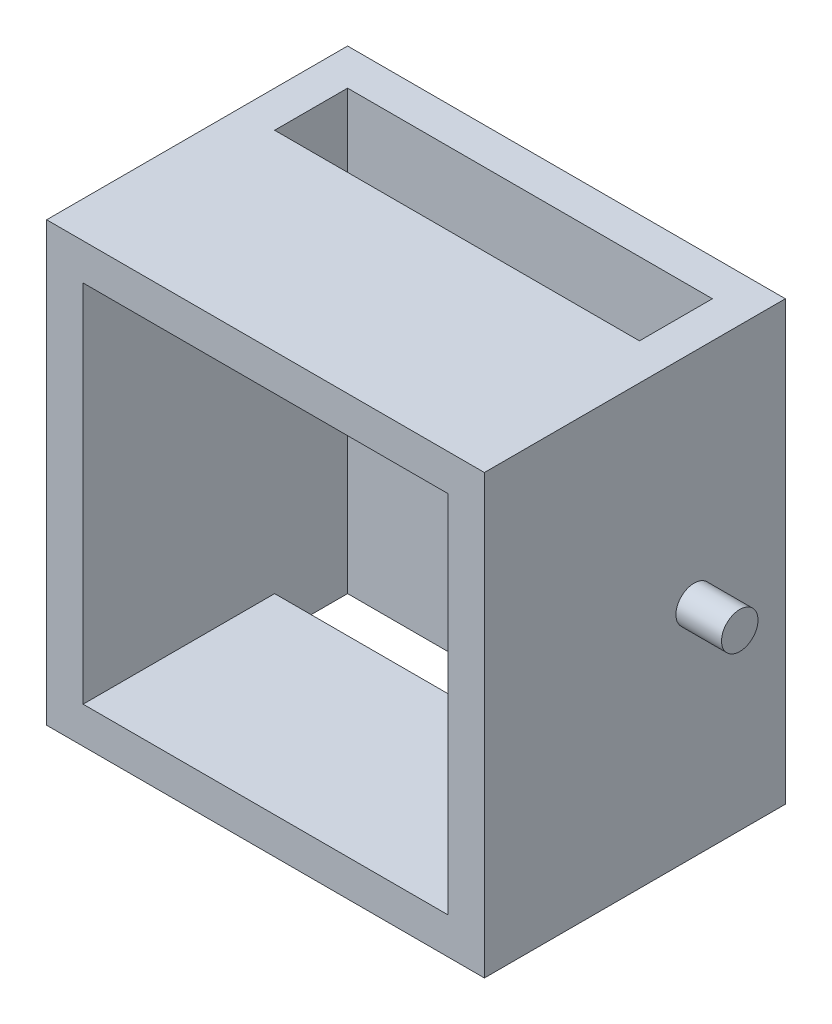
SolidWorks part; units mm, degrees
ref_plane "Front Plane" through (0, 0, 0) normal (0, 0, 1) x (1, 0, 0)
ref_plane "Top Plane" through (0, 0, 0) normal (0, 1, 0) x (1, 0, 0)
ref_plane "Right Plane" through (0, 0, 0) normal (1, 0, 0) x (0, 0, -1)
sketch "Sketch1" plane through (0, 0, 0) normal (0, 0, 1) x (1, 0, 0)
  line L1 (-24, -24) -> (24, -24)
  line L2 (-24, -24) -> (-24, 24)
  line L3 (-24, 24) -> (24, 24)
  line L4 (24, -24) -> (24, 24)
  line L5 (-24, -24) -> (24, 24) construction
  line L6 (-24, 24) -> (24, -24) construction
  point P0 (0, 0)
  dimension "D1" = 48
extrude "Boss-Extrude1" add sketch "Sketch1" along normal blind 33
shell "Shell1" thickness 4
sketch "Sketch2" plane through (0, 24, 0) normal (0, 1, 0) x (1, 0, 0)
  line L0 (0, 0) -> (0, -4) construction
  line L1 (-20, -12) -> (20, -12)
  line L2 (-20, -12) -> (-20, -4)
  line L3 (-20, -4) -> (20, -4)
  line L4 (20, -12) -> (20, -4)
  line L5 (-20, -12) -> (20, -4) construction
  line L6 (-20, -4) -> (20, -12) construction
  point P0 (0, -8)
  dimension "D1" = 40
  dimension "D2" = 4
  dimension "D3" = 8
extrude "Cut-Extrude1" cut sketch "Sketch2" against normal through all
sketch "Sketch3" plane through (24, 0, 0) normal (1, 0, 0) x (0, 0, -1)
  line L1 (0, -24) -> (0, 24) construction
  line L2 (0, 0) -> (-10, 0) construction
  circle A0 centre (-10, 0) radius 2
  dimension "D1" = 4
  dimension "D3" = 10
extrude "Boss-Extrude2" add sketch "Sketch3" along normal blind 5
mirror "Mirror1" about plane through (0, 0, 0) normal (1, 0, 0) of "Boss-Extrude2"
